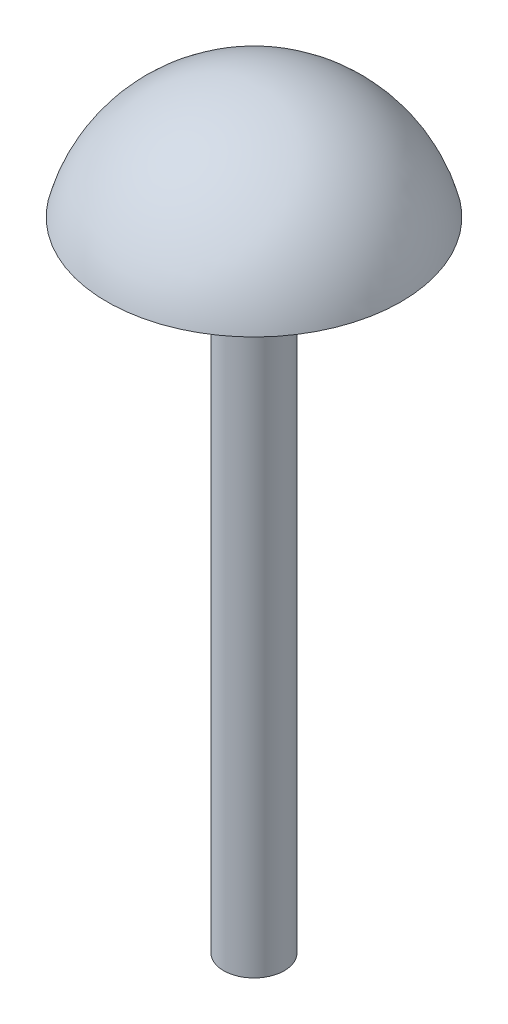
SolidWorks part; units mm, degrees
ref_plane "Front Plane" through (0, 0, 0) normal (0, 0, 1) x (1, 0, 0)
ref_plane "Top Plane" through (0, 0, 0) normal (0, 1, 0) x (1, 0, 0)
ref_plane "Right Plane" through (0, 0, 0) normal (1, 0, 0) x (0, 0, -1)
sketch "Sketch1" plane through (0, 0, 0) normal (0, 0, 1) x (1, 0, 0)
  line L0 (0, 0) -> (0.608, 0)
  line L1 (0.608, 0) -> (0.608, 12.7396)
  line L2 (0.608, 12.7396) -> (2.9373, 12.7396)
  line L3 (0, 0) -> (0, 15.018)
  arc A0 (0, 15.018) -> (2.9373, 12.7396) centre (0, 11.9854) cw
revolve "Revolve1" add sketch "Sketch1" angle 360 about L3
